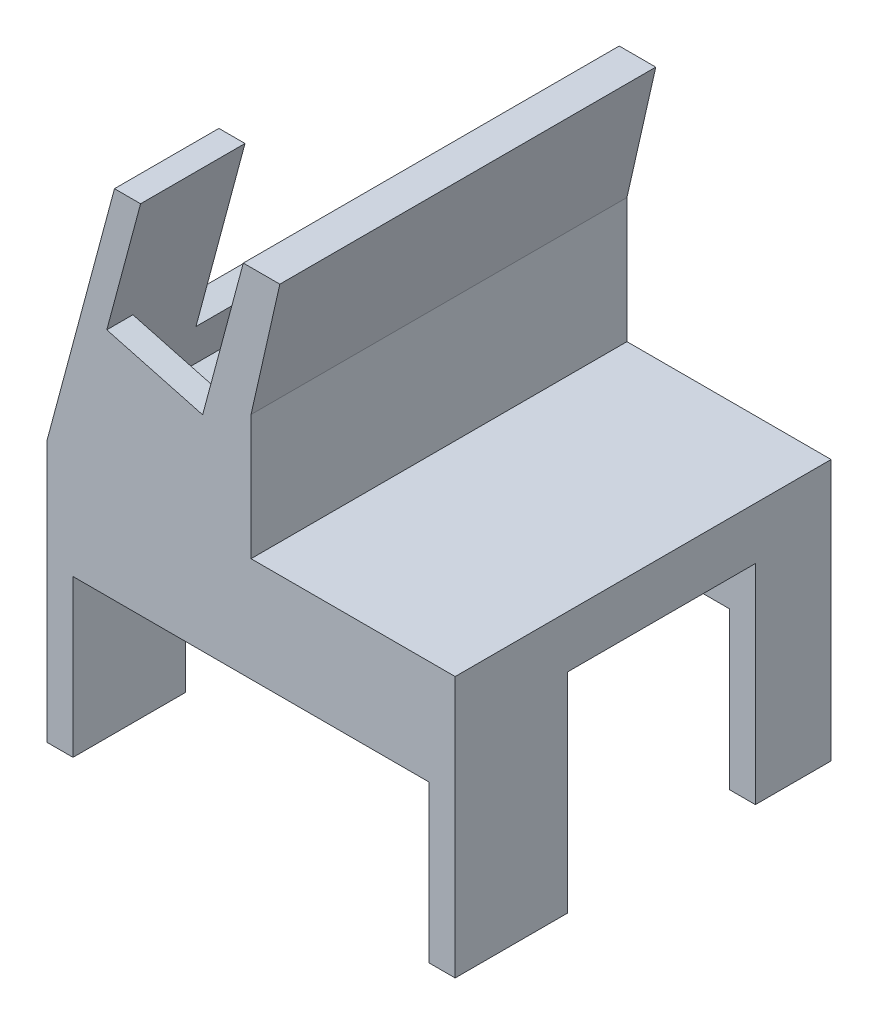
SolidWorks part; units mm, degrees
ref_plane "前基準面" through (0, 0, 0) normal (0, 0, 1) x (1, 0, 0)
ref_plane "上基準面" through (0, 0, 0) normal (0, 1, 0) x (1, 0, 0)
ref_plane "右基準面" through (0, 0, 0) normal (1, 0, 0) x (0, 0, -1)
sketch "草圖1" plane through (0, 0, 0) normal (0, 0, 1) x (1, 0, 0)
  line L1 (-56.4104, -6.4286) -> (-51.4104, -6.4286)
  line L2 (-56.4104, -6.4286) -> (-56.4104, -36.4286)
  line L3 (-56.4104, -36.4286) -> (-51.4104, -36.4286)
  line L4 (-51.4104, -6.4286) -> (-51.4104, -36.4286)
  line L5 (-56.4104, -6.4286) -> (21.7764, -6.4286)
  line L6 (-56.4104, -6.4286) -> (-56.4104, 13.5714)
  line L7 (-56.4104, 13.5714) -> (21.7764, 13.5714)
  line L8 (21.7764, -6.4286) -> (21.7764, 13.5714)
  line L9 (21.7764, -6.4286) -> (16.7764, -6.4286)
  line L10 (21.7764, -6.4286) -> (21.7764, -36.4286)
  line L11 (21.7764, -36.4286) -> (16.7764, -36.4286)
  line L12 (16.7764, -6.4286) -> (16.7764, -36.4286)
  dimension "D1" = 30
  dimension "D2" = 5
  dimension "D3" = 5
  dimension "D4" = 20
extrude "填料-伸長1" add sketch "草圖1" along normal blind 72 contours L5 L8 L7 L6 L1 | L5 L12 L11 L10
sketch "草圖2" plane through (0, -6.4286, 0) normal (0, -1, 0) x (1, 0, 0)
  line L0 (-51.4104, 72) -> (-51.4104, 0) construction
  line L1 (-51.4104, 14.5) -> (16.7764, 14.5)
  line L2 (-51.4104, 14.5) -> (-51.4104, 50.5)
  line L3 (-51.4104, 50.5) -> (16.7764, 50.5)
  line L4 (16.7764, 14.5) -> (16.7764, 50.5)
  line L5 (16.7764, 72) -> (16.7764, 0) construction
  line L6 (-51.4104, 72) -> (16.7764, 72) construction
  line L7 (-51.4104, 0) -> (16.7764, 0) construction
  dimension "D1" = 21.5
  dimension "D2" = 14.5
extrude "除料-伸長1" cut sketch "草圖2" against normal blind 10
sketch "草圖3" plane through (0, -36.4286, 0) normal (0, -1, 0) x (1, 0, 0)
  line L0 (-51.4104, 72) -> (-51.4104, 0) construction
  line L1 (-51.4104, 14.5) -> (-56.4104, 14.5)
  line L2 (-51.4104, 14.5) -> (-51.4104, 50.5)
  line L3 (-51.4104, 50.5) -> (-56.4104, 50.5)
  line L4 (-56.4104, 14.5) -> (-56.4104, 50.5)
  line L5 (-56.4104, 72) -> (-56.4104, 0) construction
  line L6 (-56.4104, 0) -> (-51.4104, 0) construction
  line L7 (-56.4104, 72) -> (-51.4104, 72) construction
  point P10 (-53.9104, 50.5)
  dimension "D1" = 14.5
  dimension "D2" = 21.5
extrude "除料-伸長3" cut sketch "草圖3" against normal blind 40
sketch "草圖4" plane through (0, -36.4286, 0) normal (0, -1, 0) x (1, 0, 0)
  line L0 (16.7764, 72) -> (16.7764, 0) construction
  line L1 (16.7764, 50.5) -> (21.7764, 50.5)
  line L2 (16.7764, 50.5) -> (16.7764, 14.5)
  line L3 (16.7764, 14.5) -> (21.7764, 14.5)
  line L4 (21.7764, 50.5) -> (21.7764, 14.5)
  line L5 (21.7764, 72) -> (21.7764, 0) construction
  line L6 (21.7764, 72) -> (16.7764, 72) construction
  line L7 (21.7764, 0) -> (16.7764, 0) construction
  dimension "D1" = 21.5
  dimension "D2" = 14.5
extrude "除料-伸長4" cut sketch "草圖4" against normal blind 40
ref_plane "平面1" through (0, 0, 72) normal (0, 0, 1) x (1, 0, 0)
sketch "草圖5" plane through (0, 0, 72) normal (0, 0, 1) x (1, 0, 0)
  line L0 (-56.4104, 13.5714) -> (-43.4694, 61.8677)
  line L1 (-43.4694, 61.8677) -> (-38.4694, 61.8677)
  line L2 (-56.4104, 13.5714) -> (21.7764, 13.5714) construction
  line L3 (-38.4694, 61.8677) -> (-44.9399, 37.7196)
  line L4 (-44.9399, 37.7196) -> (-26.5873, 32.802)
  line L5 (-26.5873, 32.802) -> (-18.7992, 61.8677)
  line L6 (-18.7992, 61.8677) -> (-11.7992, 61.8677)
  line L9 (-17.317, 13.5714) -> (-56.4104, 13.5714)
  line L10 (-17.317, 13.5714) -> (-17.317, 37.4842)
  line L11 (-17.317, 37.4842) -> (-11.7992, 61.8677)
  dimension "D1" = 50
  dimension "D2" = 75
  dimension "D3" = 19
  dimension "D4" = 5
  dimension "D5" = 25
  dimension "D6" = 7
  dimension "D7" = 25
extrude "填料-伸長2" add sketch "草圖5" against normal blind 5
sketch "草圖7" plane through (0, 0, 67) normal (0, 0, -1) x (-1, 0, 0)
  line L0 (56.4104, 13.5714) -> (43.4694, 61.8677)
  line L1 (43.4694, 61.8677) -> (38.4694, 61.8677)
  line L2 (38.4694, 61.8677) -> (50.0927, 18.489)
  line L3 (50.0927, 18.489) -> (31.7401, 13.5714)
  line L4 (56.4104, 13.5714) -> (17.317, 13.5714) construction
  line L5 (18.7992, 61.8677) -> (31.7401, 13.5714)
  line L6 (18.7992, 61.8677) -> (11.7992, 61.8677)
  line L7 (11.7992, 61.8677) -> (17.317, 37.4842)
  line L8 (17.317, 37.4842) -> (17.317, 13.5714)
  line L9 (17.317, 13.5714) -> (31.7401, 13.5714)
  line L10 (31.7401, 13.5714) -> (56.4104, 13.5714)
  line M11 (17.317, 13.5714) -> (56.4104, 13.5714)
  line M12 (56.4104, 13.5714) -> (43.4694, 61.8677)
  line M13 (43.4694, 61.8677) -> (38.4694, 61.8677)
  line M14 (38.4694, 61.8677) -> (44.9399, 37.7196)
  line M16 (26.5873, 32.802) -> (18.7992, 61.8677)
  line M17 (18.7992, 61.8677) -> (11.7992, 61.8677)
  line M18 (11.7992, 61.8677) -> (17.317, 37.4842)
  line M19 (17.317, 37.4842) -> (17.317, 13.5714)
  dimension "D1" = 19
extrude "填料-伸長3" add sketch "草圖7" along normal blind 67 contours L5 M16 M17 M18 M19 M11 | L2 L3 M11 M12 M13 M14
sketch "草圖8" plane through (-56.0245, 15.0117, 0) normal (-0.9659, 0.2588, 0) x (0, 0, 1)
  line L0 (72, -1.4911) -> (0, -1.4911) construction
  line L1 (0, 51.5829) -> (52, 51.5829)
  line L2 (0, 51.5829) -> (0, 13.5089)
  line L3 (0, 13.5089) -> (52, 13.5089)
  line L4 (52, 51.5829) -> (52, 13.5089)
  line L5 (72, 48.5089) -> (72, -1.4911) construction
  dimension "D1" = 15
  dimension "D2" = 20
extrude "除料-伸長5" cut sketch "草圖8" against normal blind 5 contours L1 L4 L3 L2
